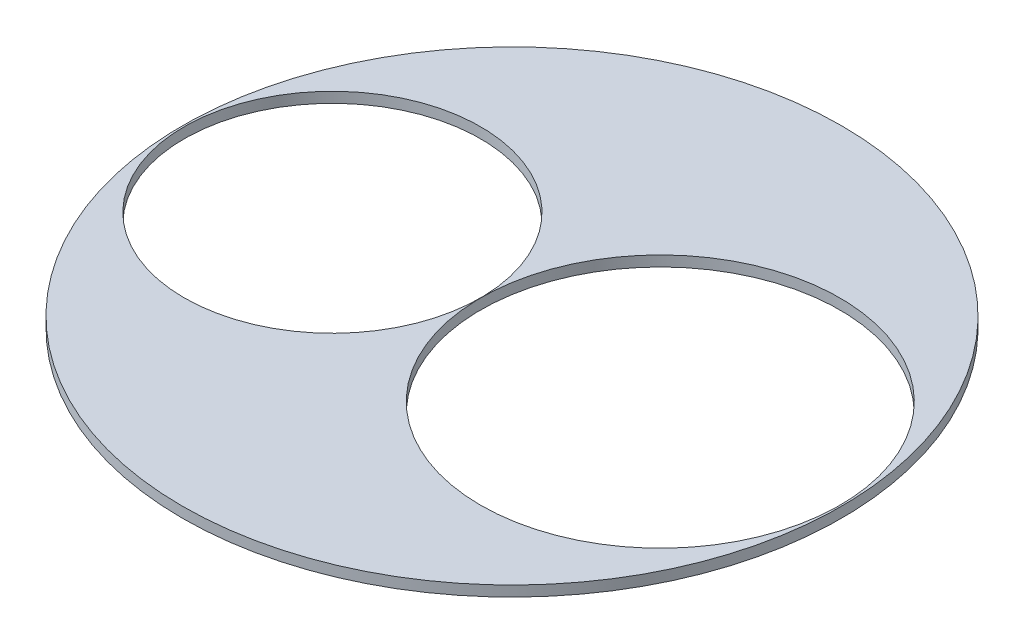
SolidWorks part; units mm, degrees
ref_plane "Front Plane" through (0, 0, 0) normal (0, 0, 1) x (1, 0, 0)
ref_plane "Top Plane" through (0, 0, 0) normal (0, 1, 0) x (1, 0, 0)
ref_plane "Right Plane" through (0, 0, 0) normal (1, 0, 0) x (0, 0, -1)
sketch "Sketch1" plane through (0, 0, 0) normal (0, 1, 0) x (1, 0, 0)
  circle A0 centre (0, 0) radius 1200
  circle A1 centre (539.876, 0) radius 654.05
  circle A2 centre (-653.9494, 0) radius 539.75
  point P7 (539.8506, 0)
  dimension "D1" = 2400
  dimension "D2" = 1308.1
  dimension "D3" = 1079.5
  dimension "D4" = 1193.8254
extrude "Boss-Extrude1" add sketch "Sketch1" along normal blind 38.1
